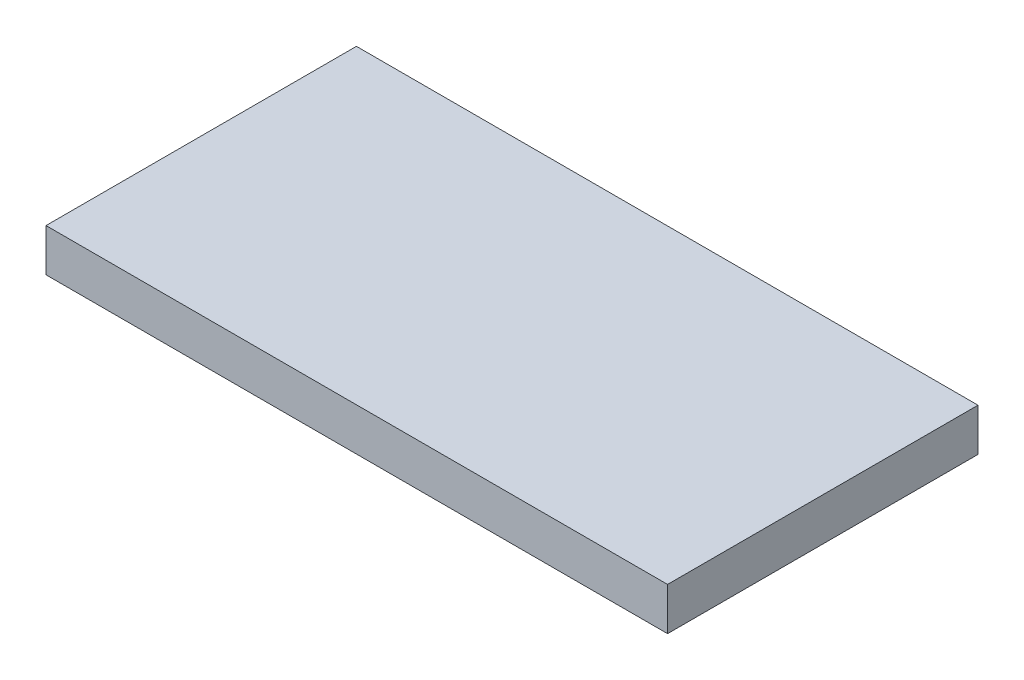
SolidWorks part; units mm, degrees
material "CA"
ref_plane "Front Plane" through (0, 0, 0) normal (0, 0, 1) x (1, 0, 0)
ref_plane "Top Plane" through (0, 0, 0) normal (0, 1, 0) x (1, 0, 0)
ref_plane "Right Plane" through (0, 0, 0) normal (1, 0, 0) x (0, 0, -1)
sketch "Sketch1" plane through (0, 0, 0) normal (0, 1, 0) x (1, 0, 0)
  line L1 (0, 0) -> (192.0875, 0)
  line L2 (0, 0) -> (0, 95.9358)
  line L3 (0, 95.9358) -> (192.0875, 95.9358)
  line L4 (192.0875, 0) -> (192.0875, 95.9358)
  dimension "D1" = 192.0875
  dimension "D2" = 95.9358
extrude "Boss-Extrude1" add sketch "Sketch1" along normal blind 13.1826
sketch "Sketch2" plane through (0, 0, 0) normal (0, -1, 0) x (1, 0, 0)
  line L0 (0, -95.9358) -> (0, 0) construction
  line L1 (12.954, -12.954) -> (179.1335, -12.954)
  line L2 (12.954, -12.954) -> (12.954, -82.9818)
  line L3 (12.954, -82.9818) -> (179.1335, -82.9818)
  line L4 (179.1335, -12.954) -> (179.1335, -82.9818)
  line L5 (192.0875, 0) -> (192.0875, -95.9358) construction
  line L6 (0, 0) -> (192.0875, 0) construction
  line L7 (192.0875, -95.9358) -> (0, -95.9358) construction
  dimension "D1" = 12.954
  dimension "D2" = 12.954
  dimension "D3" = 12.954
  dimension "D4" = 12.954
extrude "Cut-Extrude1" cut sketch "Sketch2" against normal blind 7.874
sketch "Sketch3" plane through (0, 0, 0) normal (0, -1, 0) x (1, 0, 0)
  line L0 (0, -47.9679) -> (192.0875, -47.9679) construction
  line L1 (0, -95.9358) -> (0, 0) construction
  line L2 (192.0875, 0) -> (192.0875, -95.9358) construction
  line L3 (12.954, -12.954) -> (12.954, -82.9818) construction
  line L4 (192.0875, -95.9358) -> (0, -95.9358) construction
  line L5 (96.0438, 0) -> (96.0438, -95.9358) construction
  line L6 (0, 0) -> (192.0875, 0) construction
  circle A0 centre (12.7, -85.7758) radius 1.27
  circle A1 centre (12.7, -10.16) radius 1.27
  circle A2 centre (179.3875, -85.7758) radius 1.27
  circle A3 centre (179.3875, -10.16) radius 1.27
  dimension "D1" = 2.54
  dimension "D2" = 0.254
  dimension "D3" = 10.16
extrude "Cut-Extrude2" cut sketch "Sketch3" against normal blind 7.874
sketch "Sketch4" plane through (0, 7.874, 0) normal (0, -1, 0) x (-1, 0, 0)
  line L0 (-12.954, 82.9818) -> (-179.1335, 82.9818) construction
  line L1 (-66.294, 45.6692) -> (-82.0928, 45.6692)
  line L2 (-66.294, 45.6692) -> (-66.294, 53.9496)
  line L3 (-66.294, 53.9496) -> (-82.0928, 53.9496)
  line L4 (-82.0928, 45.6692) -> (-82.0928, 53.9496)
  line L5 (-12.954, 12.954) -> (-12.954, 82.9818) construction
  dimension "D1" = 15.7988
  dimension "D2" = 8.2804
  dimension "D3" = 29.0322
  dimension "D4" = 53.34
extrude "Boss-Extrude2" add sketch "Sketch4" along normal blind 9.8298
sketch "Sketch5" plane through (0, 7.874, 0) normal (0, -1, 0) x (-1, 0, 0)
  line L0 (-12.954, 12.954) -> (-12.954, 82.9818) construction
  line L1 (-16.8148, 34.417) -> (-25.7048, 34.417)
  line L2 (-16.8148, 34.417) -> (-16.8148, 62.357)
  line L3 (-16.8148, 62.357) -> (-25.7048, 62.357)
  line L4 (-25.7048, 34.417) -> (-25.7048, 62.357)
  line L5 (-12.954, 82.9818) -> (-179.1335, 82.9818) construction
  line L6 (-96.0438, 12.954) -> (-96.0438, 82.9818) construction
  line L7 (-179.1335, 12.954) -> (-12.954, 12.954) construction
  line L8 (-12.954, 82.9818) -> (-179.1335, 82.9818) construction
  line L9 (-175.2727, 62.357) -> (-166.3827, 62.357)
  line L10 (-166.3827, 34.417) -> (-166.3827, 62.357)
  line L11 (-175.2727, 34.417) -> (-166.3827, 34.417)
  line L12 (-175.2727, 34.417) -> (-175.2727, 62.357)
  dimension "D1" = 8.89
  dimension "D2" = 27.94
  dimension "D3" = 3.8608
  dimension "D4" = 20.6248
extrude "Boss-Extrude3" add sketch "Sketch5" along normal blind 7.874
sketch "Sketch6" plane through (0, 0, 0) normal (0, -1, 0) x (-1, 0, 0)
  line L1 (-12.954, 12.954) -> (-12.954, 82.9818) construction
  line L2 (0, 47.9679) -> (-192.0875, 47.9679) construction
  line L3 (0, 95.9358) -> (0, 0) construction
  line L4 (-192.0875, 0) -> (-192.0875, 95.9358) construction
  line L5 (-96.0438, 95.9358) -> (-96.0438, 0) construction
  line L6 (-192.0875, 95.9358) -> (0, 95.9358) construction
  line L7 (0, 0) -> (-192.0875, 0) construction
  line L8 (-179.1335, 12.954) -> (-12.954, 12.954) construction
  circle A0 centre (-8.2804, 17.8562) radius 1.0668
  circle A1 centre (-183.8071, 17.8562) radius 1.0668 construction
  circle A2 centre (-183.8071, 78.0796) radius 1.0668
  dimension "D1" = 2.1336
  dimension "D2" = 4.9022
  dimension "D3" = 4.6736
extrude "Boss-Extrude4" add sketch "Sketch6" along normal blind 3.683
fillet "Fillet1" radius 5.08 4 edges at (179.1335, 3.937, -12.954) (179.1335, 3.937, -82.9818) (12.954, 3.937, -82.9818) (12.954, 3.937, -12.954)
fillet "Fillet2" radius 0.635 2 edges at (183.8071, -3.683, -79.1464) (8.2804, -3.683, -18.923)
